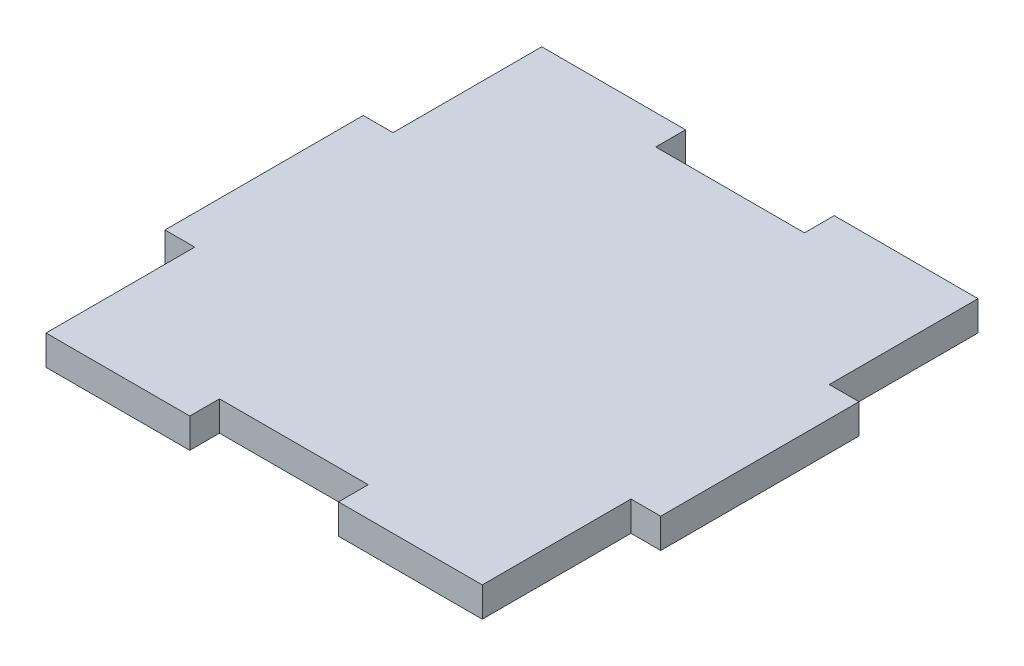
SolidWorks part; units mm, degrees
ref_plane "前视基准面" through (0, 0, 0) normal (0, 0, 1) x (1, 0, 0)
ref_plane "上视基准面" through (0, 0, 0) normal (0, 1, 0) x (1, 0, 0)
ref_plane "右视基准面" through (0, 0, 0) normal (1, 0, 0) x (0, 0, -1)
sketch "草图1" plane through (0, 0, 0) normal (0, 1, 0) x (1, 0, 0)
  line L0 (22, 25) -> (22, -25) construction
  line L1 (-25, 25) -> (25, 25) construction
  line L2 (-25, 25) -> (-25, -25) construction
  line L3 (-25, -25) -> (25, -25) construction
  line L4 (25, 25) -> (25, -25) construction
  line L5 (0, -25) -> (0, 25) construction
  line L6 (-25, 0) -> (25, 0) construction
  line L7 (-25, 22) -> (25, 22) construction
  line L8 (22, 25) -> (22, 10)
  line L9 (22, 10) -> (25, 10)
  line L10 (25, 10) -> (25, -10)
  line L11 (22, 25) -> (7.5, 25)
  line L12 (7.5, 25) -> (7.5, 22)
  line L13 (7.5, 22) -> (-7.5, 22)
  line L14 (-25, 10) -> (-25, -10)
  line L15 (-22, 10) -> (-25, 10)
  line L16 (-22, 25) -> (-22, 10)
  line L17 (-22, 25) -> (-7.5, 25)
  line L18 (-7.5, 25) -> (-7.5, 22)
  line L19 (22, -10) -> (25, -10)
  line L20 (22, -25) -> (22, -10)
  line L21 (22, -25) -> (7.5, -25)
  line L22 (7.5, -25) -> (7.5, -22)
  line L23 (7.5, -22) -> (-7.5, -22)
  line L24 (-7.5, -25) -> (-7.5, -22)
  line L25 (-22, -25) -> (-7.5, -25)
  line L26 (-22, -25) -> (-22, -10)
  line L27 (-22, -10) -> (-25, -10)
  circle A0 centre (0, 0) radius 4.2 construction
  circle A1 centre (0, 0) radius 10 construction
  point P0 (0, 0)
  point P21 (0, 22)
  dimension "D1" = 8.4
  dimension "D2" = 20
  dimension "D3" = 50
  dimension "D4" = 50
  dimension "D5" = 3
  dimension "D6" = 3
  dimension "D7" = 20
  dimension "D8" = 15
extrude "凸台-拉伸1" add sketch "草图1" along normal blind 3
